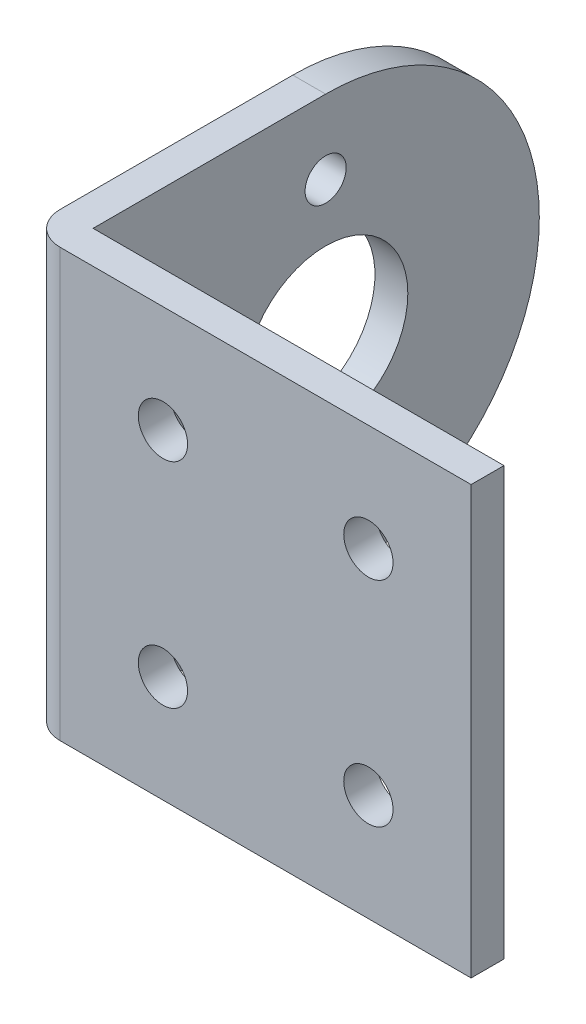
SolidWorks part; units mm, degrees
material "ABS"
ref_plane "Plan de face" through (0, 0, 0) normal (0, 0, 1) x (1, 0, 0)
ref_plane "Plan de dessus" through (0, 0, 0) normal (0, 1, 0) x (1, 0, 0)
ref_plane "Plan de droite" through (0, 0, 0) normal (1, 0, 0) x (0, 0, -1)
sketch "Esquisse1" plane through (0, 0, 0) normal (0, 0, 1) x (1, 0, 0)
  line L0 (12.5, 13) -> (-12.5, 13)
  line L1 (-12.5, 13) -> (-12.5, -13)
  line L2 (-12.5, -13) -> (12.5, -13)
  line L3 (12.5, -13) -> (12.5, 13)
  line L4 (-12.5, 0) -> (12.5, 0) construction
  line L5 (0, -13) -> (0, 13) construction
  circle A16 centre (-6.25, 6.5) radius 1.5
  circle A17 centre (6.25, 6.5) radius 1.5
  circle A18 centre (6.25, -6.5) radius 1.5
  circle A19 centre (-6.25, -6.5) radius 1.5
  point P32 (0, 0)
  dimension "D5" = 6.5
  dimension "D3" = 3
  dimension "D1" = 25
  dimension "D2" = 26
  dimension "D4" = 6.25
extrude "Boss.-Extru.1" add sketch "Esquisse1" along normal blind 2
sketch "Esquisse2" plane through (0, 13, 0) normal (0, 1, 0) x (1, 0, 0)
  line L0 (-12.5, -2) -> (12.5, -2)
  line L1 (12.5, -2) -> (12.5, 0)
  line L2 (12.5, 0) -> (-12.5, 0)
  line L3 (-12.5, 0) -> (-12.5, 14.15)
  line L4 (-12.5, 14.15) -> (-14.5, 14.15)
  line L5 (-14.5, 14.15) -> (-14.5, 0)
  line L6 (12.5, -2) -> (12.5, 0) construction
  line L7 (12.5, 0) -> (-12.5, 0) construction
  line L8 (12.5, -2) -> (-12.5, -2) construction
  arc A0 (-14.5, 0) -> (-12.5, -2) centre (-12.5, 0) ccw
  dimension "D1" = 2
  dimension "D2" = 16.15
extrude "Boss.-Extru.2" add sketch "Esquisse2" against normal up to surface (26 mm away) up to face at (0, -13, 1)
sketch "Esquisse5" plane through (-14.5, 0, 0) normal (-1, 0, 0) x (0, 0, 1)
  line L4 (-14.15, 13) -> (0, 13) construction
  line L5 (0, -13) -> (-14.15, -13) construction
  line L6 (-14.15, -13) -> (-14.15, 13)
  arc A1 (-14.15, -13) -> (-14.15, 13) centre (-14.15, 0) cw
extrude "Boss.-Extru.3" add sketch "Esquisse5" against normal up to surface (2 mm away) up to face at (-12.5, 0, -7.075)
sketch "Esquisse6" plane through (-14.5, 0, 0) normal (-1, 0, 0) x (0, 0, 1)
  circle A0 centre (-14.15, 0) radius 5
  arc A1 (-14.15, 13) -> (-14.15, -13) centre (-14.15, 0) ccw construction
  dimension "D1" = 10
sketch "Esquisse7" plane through (0, 0, 0) normal (0, 0, -1) x (-1, 0, 0)
  circle A0 centre (-6.25, -6.5) radius 1.5 construction
  circle A1 centre (6.25, -6.5) radius 1.5 construction
  circle A2 centre (6.25, 6.5) radius 1.5 construction
  circle A3 centre (-6.25, 6.5) radius 1.5 construction
  circle A4 centre (-6.25, -6.5) radius 1.5
  circle A5 centre (6.25, -6.5) radius 1.5
  circle A6 centre (6.25, 6.5) radius 1.5
  circle A7 centre (-6.25, 6.5) radius 1.5
extrude "Enlèv. mat.-Extru.1" cut sketch "Esquisse7" against normal through all
extrude "Enlèv. mat.-Extru.2" cut sketch "Esquisse6" against normal through all
sketch "Esquisse8" plane through (-14.5, 0, 0) normal (-1, 0, 0) x (0, 0, 1)
  line L0 (-14.15, -8.5) -> (-14.15, 8.5) construction
  line L1 (0, 0) -> (-27.15, 0) construction
  circle A0 centre (-14.15, 8.5) radius 1.25
  circle A2 centre (-14.15, 0) radius 5 construction
  arc A3 (-14.15, 13) -> (-14.15, -13) centre (-14.15, 0) ccw construction
  circle A4 centre (-14.15, -8.5) radius 1.25
  point P5 (-14.15, 0)
  dimension "D1" = 2.5
  dimension "D2" = 8.5
extrude "Enlèv. mat.-Extru.3" cut sketch "Esquisse8" against normal through all
